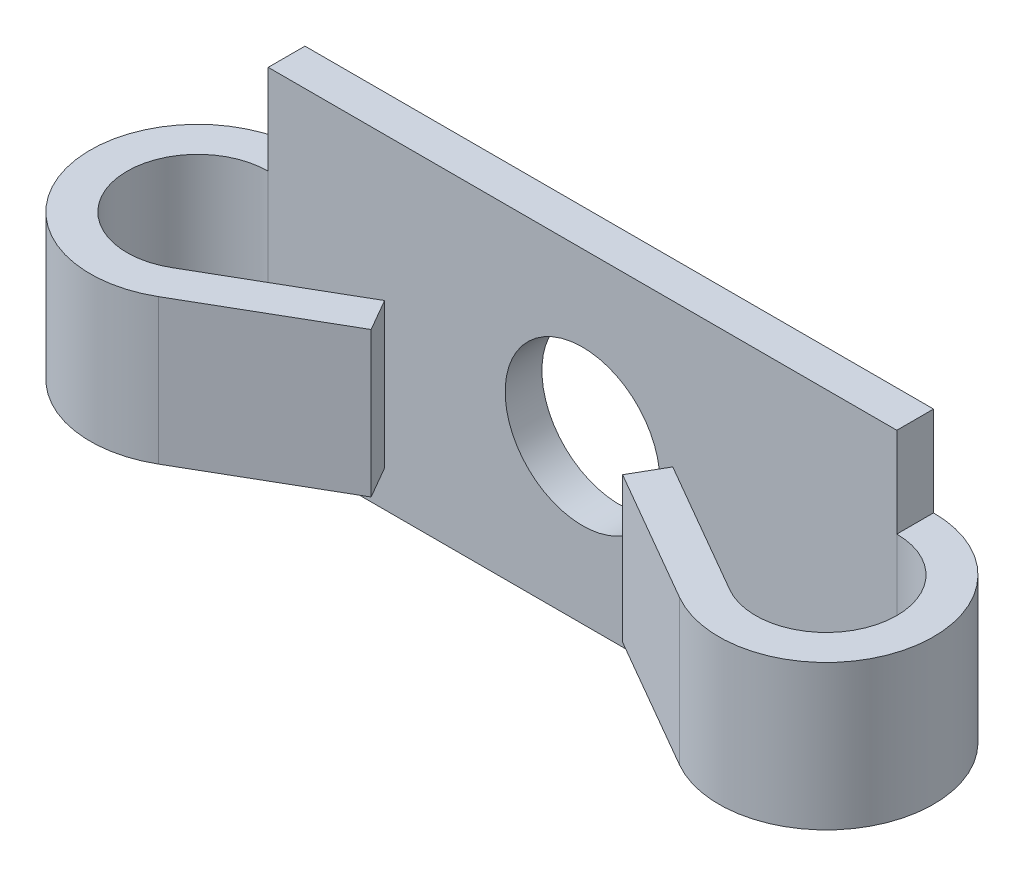
SolidWorks part; units mm, degrees
ref_plane "Спереди" through (0, 0, 0) normal (0, 0, 1) x (1, 0, 0)
ref_plane "Сверху" through (0, 0, 0) normal (0, 1, 0) x (1, 0, 0)
ref_plane "Справа" through (0, 0, 0) normal (1, 0, 0) x (0, 0, -1)
sketch "Эскиз1" plane through (0, 0, 0) normal (0, 0, 1) x (1, 0, 0)
  line L1 (-16.25, -8.4) -> (16.25, -8.4)
  line L2 (-16.25, -8.4) -> (-16.25, 8.4)
  line L3 (-16.25, 8.4) -> (16.25, 8.4)
  line L4 (16.25, -8.4) -> (16.25, 8.4)
  line L5 (-16.25, -8.4) -> (16.25, 8.4) construction
  line L6 (-16.25, 8.4) -> (16.25, -8.4) construction
  circle A0 centre (0, 0) radius 4
  point P0 (0, 0)
  dimension "D3" = 8
  dimension "D1" = 32.5
  dimension "D2" = 16.8
extrude "Бобышка-Вытянуть1" add sketch "Эскиз1" along normal blind 1.9
sketch "Эскиз3" plane through (0, 0, 0) normal (0, 1, 0) x (1, 0, 0)
  line L0 (16.25, -1.9) -> (-16.25, -1.9) construction
  line L1 (16.25, 0) -> (-16.25, 0) construction
  line L2 (-14.425, -8.711) -> (-7.45, -4.684)
  line L3 (-7.45, -4.684) -> (-6.5, -6.3294)
  line L4 (-6.5, -6.3294) -> (-13.475, -10.3564)
  line L5 (-16.25, -9.2) -> (-16.25, 0) construction
  line L6 (-4, 0) -> (-4, -1.9) construction
  line L7 (-16.25, -1.9) -> (-16.25, 0)
  arc A0 (-16.25, -1.9) -> (-14.425, -8.711) centre (-16.25, -5.55) ccw
  arc A1 (-16.25, 0) -> (-13.475, -10.3564) centre (-16.25, -5.55) ccw
  dimension "D1" = 9.2
  dimension "D2" = 30
  dimension "D3" = 2.5
extrude "Бобышка-Вытянуть2" add sketch "Эскиз3" along normal mid plane 7.5
mirror "Зеркальное отражение1" about plane through (0, 0, 0) normal (1, 0, 0) of "Бобышка-Вытянуть2"
